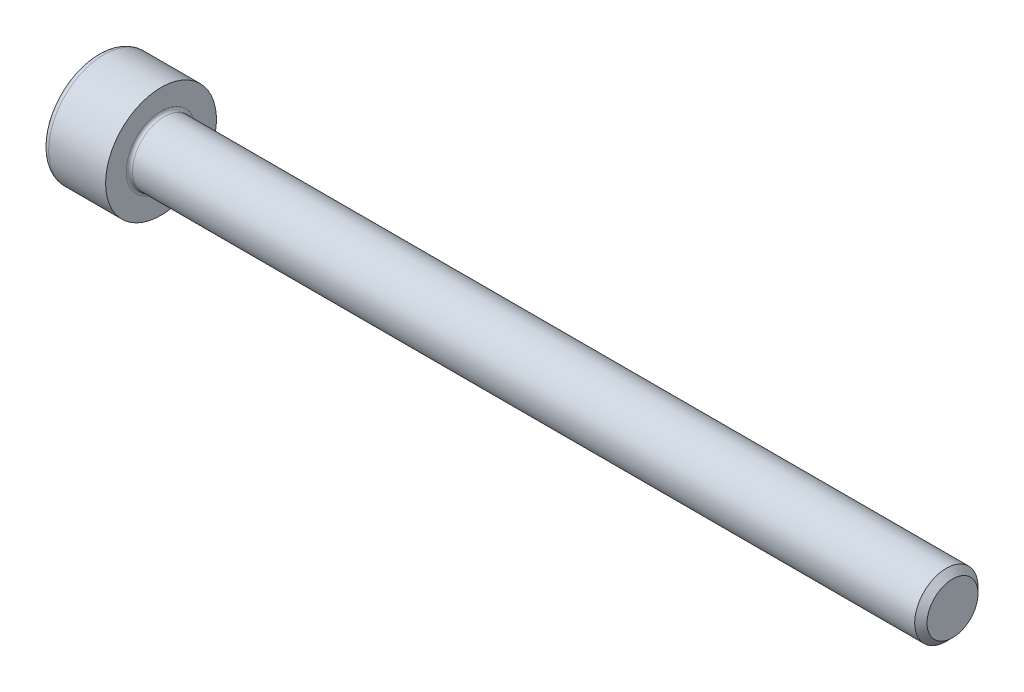
SolidWorks part; units mm, degrees
revolve "Base-Revolve" add sketch "BodySke"
sketch "BodySke" plane through (0, 0, 0) normal (0, 0, 1) x (1, 0, 0)
  line L0 (0, 0) -> (0, 3.5)
  line L1 (0, 3.5) -> (4, 3.5)
  line L2 (4, 3.5) -> (4, 2)
  line L3 (4, 2) -> (53.61, 2)
  line L4 (54, 1.61) -> (54, 0)
  line L5 (54, 0) -> (0, 0)
  line L6 (-31.75, 0) -> (127, 0) construction
  line L8 (54, 1.61) -> (53.61, 2)
  line L10 (54, -1.61) -> (53.61, -2) construction
  line L11 (4.7, 9.525) -> (4.7, 3.175) construction
  line L12 (34, 9.525) -> (34, 3.175) construction
  line L13 (38.0069, 9.525) -> (38.0069, 3.175) construction
  dimension "Head_ht" = 4
  dimension "Length" = 50
  dimension "Body_ch_ang" = 45
  dimension "Diameter" = 4
  dimension "Minor_dia" = 3.22
  dimension "Advance" = 0.7
  dimension "Thread_nom" = 20
  dimension "Thread_length" = 15.9931
  dimension "Head_dia" = 7
cosmetic thread "ThreadCosmetic" [suppressed]
fillet "Fillet1" radius 0.2 1 edges at (4, 0, 2)
fillet "Fillet2" radius 0.4 1 edges at (0, 0, 3.5)
ref_plane "Plane1" through (0, 0, 0) normal (0, 0, 1) x (1, 0, 0)
ref_plane "Plane2" through (0, 0, 0) normal (0, 1, 0) x (1, 0, 0)
ref_plane "Plane3" through (0, 0, 0) normal (1, 0, 0) x (0, 0, -1)
sketch "Sketch2" plane through (0, 0, 0) normal (0, 0, 1) x (1, 0, 0)
  line L0 (0, 1.51) -> (2, 1.51)
  line L1 (2, 1.51) -> (2.8718, 0)
  line L2 (-31.75, 0) -> (127, 0) construction
  line L3 (2.8718, 0) -> (0, 0)
  line L4 (0, 0) -> (0, 1.51)
  line L6 (0, 0) -> (47.625, 0) construction
  dimension "D1" = 1.51
  dimension "D2" = 60
  dimension "Depth" = 2
revolve "Hex-PreBroach" cut sketch "Sketch2" angle 360 about L6
sketch "Sketch3" plane through (0, 0, 0) normal (-1, 0, 0) x (0, 0.5, 0.866)
  line L0 (0.8718, 1.51) -> (-0.8718, 1.51)
  line L1 (-0.8718, 1.51) -> (-1.7436, 0)
  line L2 (0.8718, 1.51) -> (1.7436, 0)
  line L3 (0.8718, -1.51) -> (1.7436, 0)
  line L4 (0.8718, -1.51) -> (-0.8718, -1.51)
  line L5 (-0.8718, -1.51) -> (-1.7436, 0)
  dimension "D1" = 1.51
  dimension "D2" = 1.51
  dimension "Hex_size" = 3.02
extrude "Hex" cut sketch "Sketch3" against normal blind 2
sketch "ThdSchSke" plane through (0, 0, 0) normal (0, 0, 1) x (1, 0, 0)
  line L0 (34, -1.61) -> (33.7269, -2)
  line L1 (34, -1.61) -> (34.2731, -2)
  line L2 (34.2731, -2) -> (34.2731, -2.5)
  line L3 (-3.175, 0) -> (5.1513, 0) construction
  line L4 (0, 3.1) -> (0, -3.1) construction
  line L5 (34.2731, -2.5) -> (33.7269, -2.5)
  line L6 (33.7269, -2.5) -> (33.7269, -2)
  dimension "Thread_minor" = 3.22
  dimension "Diameter" = 4
  dimension "Start" = 34
revolve "ThreadSchematic" [suppressed] cut sketch "ThdSchSke" angle 360 about L3
pattern_linear "ThdSchPat" [suppressed]
equation "\"D2@Sketch3\" = \"Hex_size@Sketch3\" / 2"
equation "\"D1@Sketch3\" = \"Hex_size@Sketch3\" / 2"
equation "\"D1@Sketch2\" = \"Hex_size@Sketch3\" / 2"
equation "\"Thread_minor@ThreadCosmetic\"  =  \"Minor_dia@BodySke\""
equation "\"Depth@Sketch2\" =  \"Key_eng@Hex\""
equation "\"Thread_length@ThreadCosmetic\" = ((sgn( (\"Length@BodySke\" - \"Advance@BodySke\" * 3.0) - \"Thread_nom@BodySke\" )-1)*( (\"Length@BodySke\" - \"Advance@BodySke\" * 3.0) - \"Thread_nom@BodySke\" ))/-2+ \"Thread_nom@BodySke\""
equation "\"Thread_minor@ThdSchSke\" = \"Minor_dia@BodySke\""
equation "\"Diameter@ThdSchSke\" = \"Diameter@BodySke\""
equation "\"Overcut@ThdSchSke\" = \"Diameter@BodySke\" * 1.25"
equation "\"Start@ThdSchSke\" = \"Head_ht@BodySke\" + \"Length@BodySke\" - \"Thread_length@ThreadCosmetic\"  '---Non-countersunk---"
equation "\"Num_threads@ThdSchPat\" = int( \"Thread_length@ThreadCosmetic\" / \"Advance@BodySke\" + 0.999 )  + 1"
equation "\"Advance@ThdSchPat\" = \"Thread_length@ThreadCosmetic\" /  (\"Num_threads@ThdSchPat\" - 1) 'relax it"
equation "\"Num_threads@ThdSchPat\" = \"Num_threads@ThdSchPat\" - sgn( \"Num_threads@ThdSchPat\" - 1) '---chamfered tips only---"
